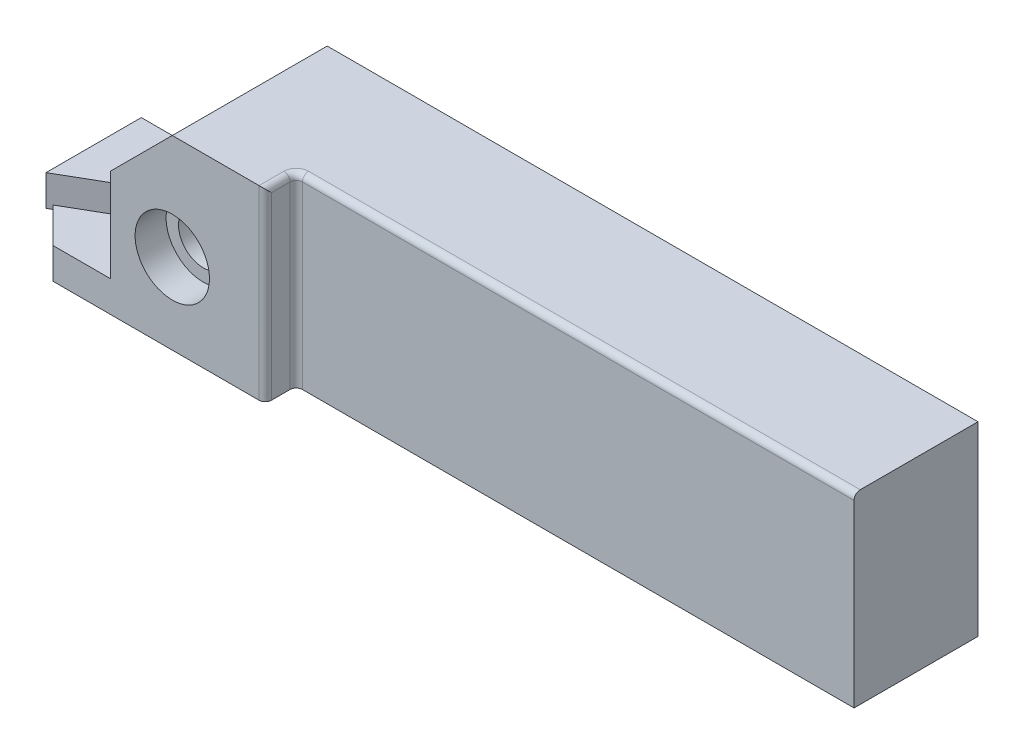
SolidWorks part; units mm, degrees
ref_plane "前视基准面" through (0, 0, 0) normal (0, 0, 1) x (1, 0, 0)
ref_plane "上视基准面" through (0, 0, 0) normal (0, 1, 0) x (1, 0, 0)
ref_plane "右视基准面" through (0, 0, 0) normal (1, 0, 0) x (0, 0, -1)
sketch "草图1" plane through (0, 0, 0) normal (0, 0, 1) x (1, 0, 0)
  line L1 (-60, 15) -> (50, 15)
  line L2 (-60, 15) -> (-60, -15)
  line L3 (-60, -15) -> (50, -15)
  line L4 (50, 15) -> (50, -15)
  point P0 (0, 0)
  dimension "D1" = 110
  dimension "D2" = 30
  dimension "D3" = 60
extrude "凸台-拉伸1" add sketch "草图1" along normal blind 20
sketch "草图3" plane through (0, 0, 20) normal (0, 0, 1) x (1, 0, 0)
  line L0 (-60, -15) -> (-60, 15)
  line L1 (-60, 15) -> (-75, 15)
  line L2 (-75, 15) -> (-85, 5)
  line L3 (-85, 5) -> (-85, -10)
  line L4 (-85, -10) -> (-105, -10)
  line L5 (-105, -10) -> (-105, -15)
  line L6 (-105, -15) -> (-60, -15)
  dimension "D1" = 135
  dimension "D2" = 15
  dimension "D3" = 15
  dimension "D4" = 30
  dimension "D5" = 45
  dimension "D6" = 5
extrude "凸台-拉伸2" add sketch "草图3" along normal blind 5 and the other way up to surface (20 mm away) other way up to face at (-5, 0, 0)
fillet "圆角1" radius 1 4 edges at (-60, 0, 25)
sketch "草图4" plane through (0, -15, 0) normal (0, -1, 0) x (1, 0, 0)
  line L0 (-94.2593, 25) -> (-99.9162, 19.3431)
  line L1 (-105, 25) -> (-61, 25) construction
  line L2 (-99.9162, 19.3431) -> (-90.4847, 13.8979)
  line L3 (-90.4847, 13.8979) -> (-77.6224, 13.8979)
  line L4 (-94.2593, 25) -> (-105, 25)
  line L5 (-77.6029, 10.9322) -> (-92.231, 10.9322)
  line L6 (-92.231, 10.9322) -> (-90.6098, 7.1066)
  line L7 (-94.2928, 5.5459) -> (-96.3397, 10.3763)
  line L8 (-96.3397, 10.3763) -> (-105, 15.3763)
  line L9 (-105, 0) -> (-105, 25) construction
  line L10 (-105, 25) -> (-105, 15.3763)
  arc A0 (-90.6098, 7.1066) -> (-94.2928, 5.5459) centre (-92.4513, 6.3263) cw
  arc A1 (-77.6224, 13.8979) -> (-77.6029, 10.9322) centre (-75.0048, 12.4322) cw
  dimension "D4" = 3
  dimension "D1" = 8
  dimension "D2" = 10
  dimension "D3" = 60
  dimension "D5" = 4
extrude "切除-拉伸1" cut sketch "草图4" against normal blind 20
hole_wizard "孔1" positions "3D草图1" profile "草图6" legacy
sketch3d "3D草图1"
  line L0 (-85, 5, 25) -> (-85, -10, 25) construction
  line L1 (-94.2593, -15, 25) -> (-61, -15, 25) construction
  point P0 (-75, -2, 25)
  dimension "D1" = 10
  dimension "D2" = 13
sketch "草图6" plane through (-75, -2, 25) normal (1, 0, 0) x (0, -1, 0)
  line L0 (0, 0) -> (0, 20)
  line L1 (0, 20) -> (4, 20)
  line L2 (4, 20) -> (4, 5)
  line L3 (4, 5) -> (6, 5)
  line L4 (6, 5) -> (6, 0)
  line L5 (6, 0) -> (0, 0)
  line L6 (0, 110) -> (0, -10) construction
  dimension "直径" = 8
  dimension "深度" = 20
  dimension "柱坑直径" = 12
  dimension "柱坑深度" = 5
cosmetic thread "装饰螺纹线1" parameters "D2"=24
sketch "草图7" plane through (0, -15, 0) normal (0, -1, 0) x (-1, 0, 0)
  line L0 (59, -20) -> (-50, -20) construction
  line L1 (-30, -20) -> (-50, -20)
  line L2 (-30, -20) -> (-30, 0)
  line L3 (-30, 0) -> (-50, 0)
  line L4 (-50, -20) -> (-50, 0)
  dimension "D1" = 20
extrude "切除-拉伸2" cut sketch "草图7" against normal up to next
